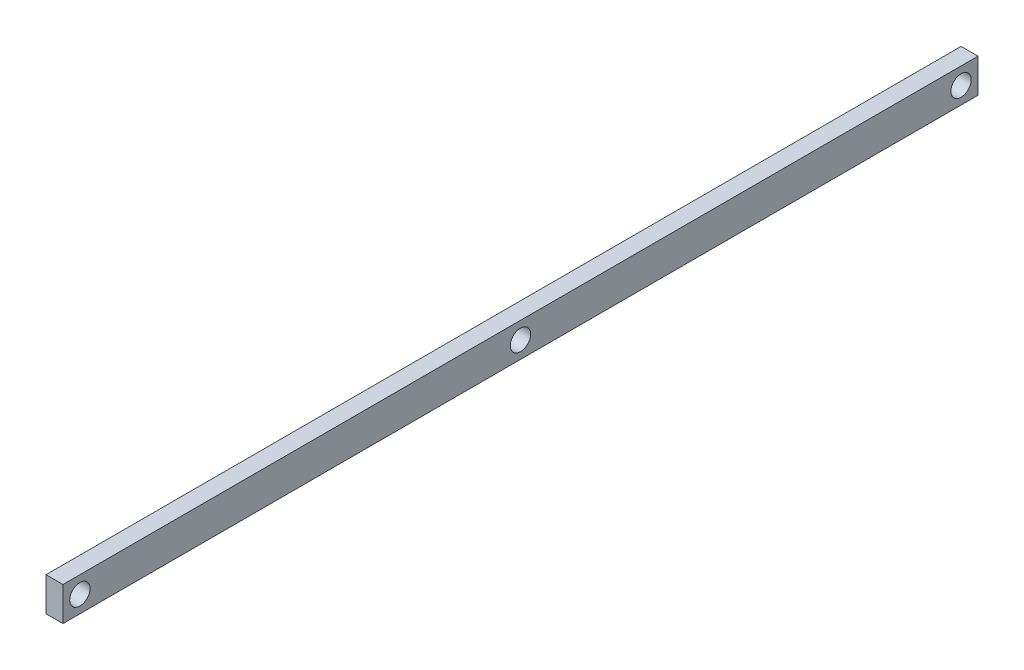
SolidWorks part; units mm, degrees
ref_plane "Front Plane" through (0, 0, 0) normal (0, 0, 1) x (1, 0, 0)
ref_plane "Top Plane" through (0, 0, 0) normal (0, 1, 0) x (1, 0, 0)
ref_plane "Right Plane" through (0, 0, 0) normal (1, 0, 0) x (0, 0, -1)
sketch "Sketch1" plane through (0, 0, 0) normal (1, 0, 0) x (0, 0, -1)
  line L1 (-135, -5) -> (135, -5)
  line L2 (-135, -5) -> (-135, 5)
  line L3 (-135, 5) -> (135, 5)
  line L4 (135, -5) -> (135, 5)
  line L5 (-135, -5) -> (135, 5) construction
  line L6 (-135, 5) -> (135, -5) construction
  point P0 (0, 0)
  dimension "D1" = 10
  dimension "D2" = 270
extrude "Boss-Extrude1" add sketch "Sketch1" along normal blind 5
sketch "Sketch2" plane through (5, 0, 0) normal (1, 0, 0) x (0, 0, -1)
  circle A0 centre (0, 0) radius 3
  circle A1 centre (130, 0) radius 3
  circle A2 centre (-130, 0) radius 3
  dimension "D1" = 2
  dimension "D2" = 2
extrude "Cut-Extrude1" cut sketch "Sketch2" against normal up to surface (5 mm away) up to face at (0, 0, 0)
